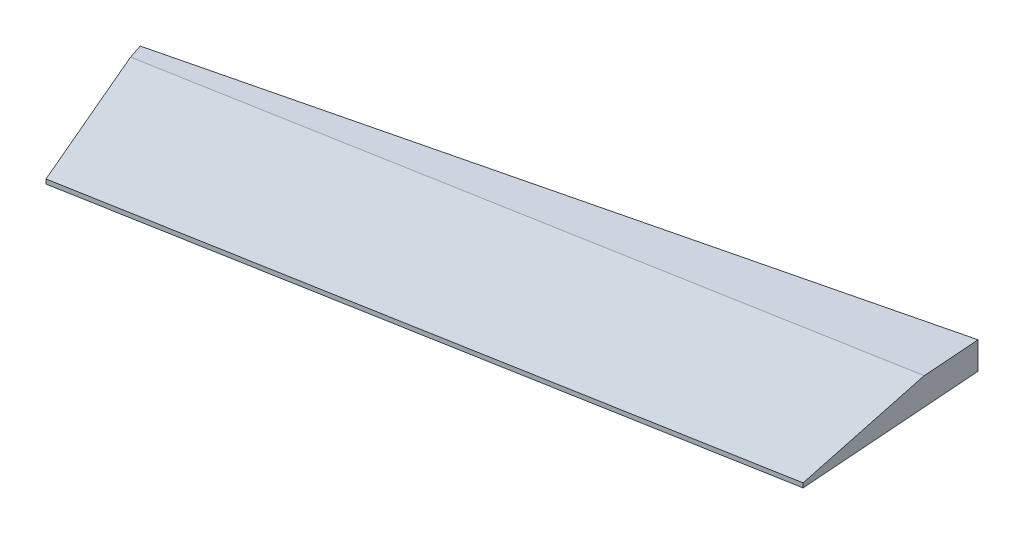
SolidWorks part; units mm, degrees
ref_plane "Front Plane" through (0, 0, 0) normal (0, 0, 1) x (1, 0, 0)
ref_plane "Top Plane" through (0, 0, 0) normal (0, 1, 0) x (1, 0, 0)
ref_plane "Right Plane" through (0, 0, 0) normal (1, 0, 0) x (0, 0, -1)
sketch "Sketch2" plane through (0, 0, 0) normal (0, 1, 0) x (1, 0, 0)
  line L0 (133.2864, -770.74) -> (147.9342, -816.0565)
  line L1 (147.9342, -816.0565) -> (356.6648, -778.5216)
  line L2 (356.6648, -778.5216) -> (352.2632, -717.2306)
  line L3 (352.2632, -717.2306) -> (133.2864, -770.74)
  point P4 (147.9342, -816.0565)
extrude "Boss-Extrude1" add sketch "Sketch2" against normal blind 8.89
chamfer "Chamfer1" distance 7.46 angle 80 1 edges at (252.2995, 0, 797.2891)
